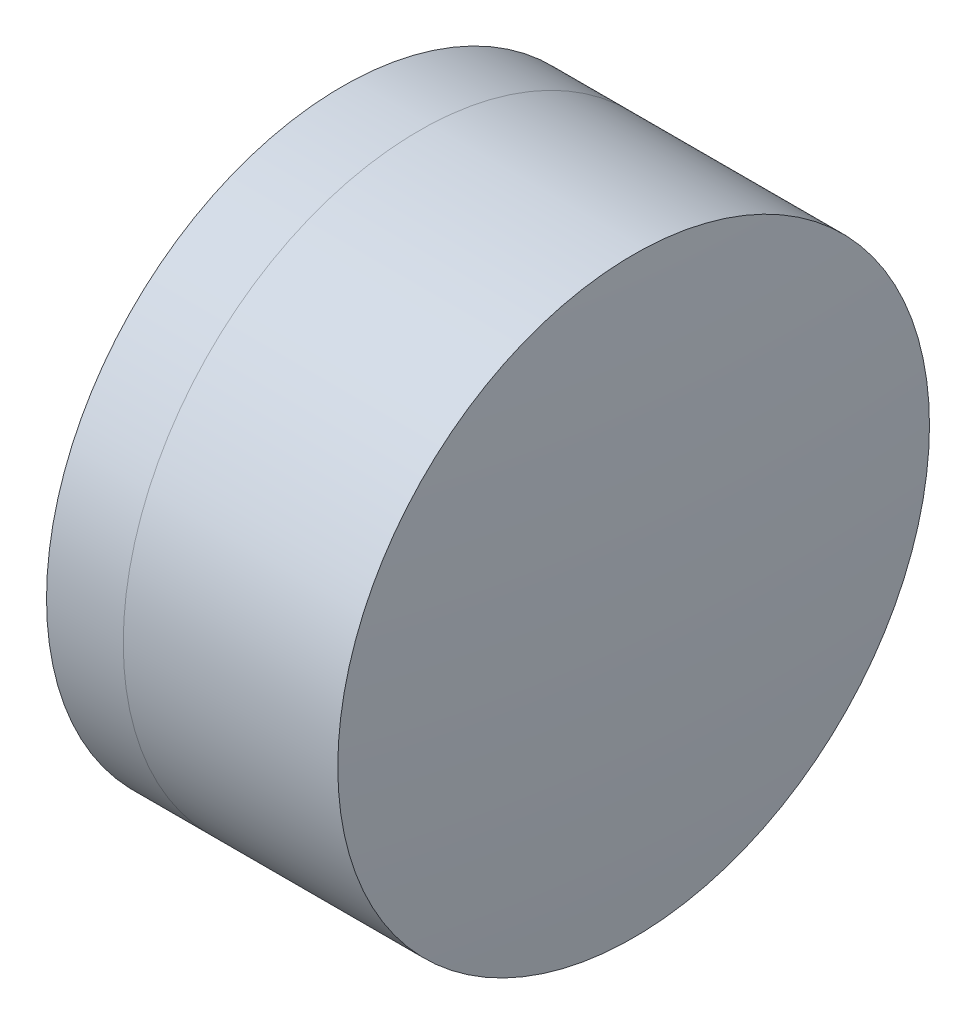
SolidWorks part; units mm, degrees
ref_plane "前视基准面" through (0, 0, 0) normal (0, 0, 1) x (1, 0, 0)
ref_plane "上视基准面" through (0, 0, 0) normal (0, 1, 0) x (1, 0, 0)
ref_plane "右视基准面" through (0, 0, 0) normal (1, 0, 0) x (0, 0, -1)
sketch "草图1" plane through (0, 0, 0) normal (0, 1, 0) x (1, 0, 0)
  line L0 (-9.7026, 0) -> (11.7646, 0) construction
  line L1 (-0.9031, -3.175) -> (-0.0797, -3.175)
  line L2 (-0.9031, 3.175) -> (-0.0797, 3.175)
  arc A0 (-0.0797, -3.175) -> (-0.0797, 3.175) centre (-5.0526, 0) ccw
  arc A1 (-0.9031, 3.175) -> (-0.9031, -3.175) centre (5.4474, 0) ccw
  point P4 (-9.7026, 0)
  point P10 (-1.6526, 0)
  point P11 (0.8474, 0)
  dimension "D3" = 7.1
  dimension "D4" = 5.9
  dimension "D1" = 3.175
  dimension "D2" = 3.175
  dimension "D5" = 2.5
revolve "旋转1" add sketch "草图1" angle 360 about L0
sketch "草图2" plane through (0, 0, 0) normal (0, 1, 0) x (1, 0, 0)
  line L0 (-0.5519, 0) -> (13.3053, 0) construction
  line L2 (-0.0797, 3.175) -> (2.2225, 3.175)
  line L3 (-0.0797, -3.175) -> (2.2225, -3.175)
  arc A0 (2.2225, -3.175) -> (2.2225, 3.175) centre (-38.0526, 0) ccw
  arc A1 (-0.0797, -3.175) -> (-0.0797, 3.175) centre (-5.0526, 0) ccw construction
  arc A2 (-0.0797, -3.175) -> (-0.0797, 3.175) centre (-5.0526, 0) ccw
  point P4 (0.8474, 0)
  point P8 (2.3474, 0)
  dimension "D1" = 40.4
  dimension "D2" = 1.5
revolve "旋转3" add sketch "草图2" angle 360 about L0
